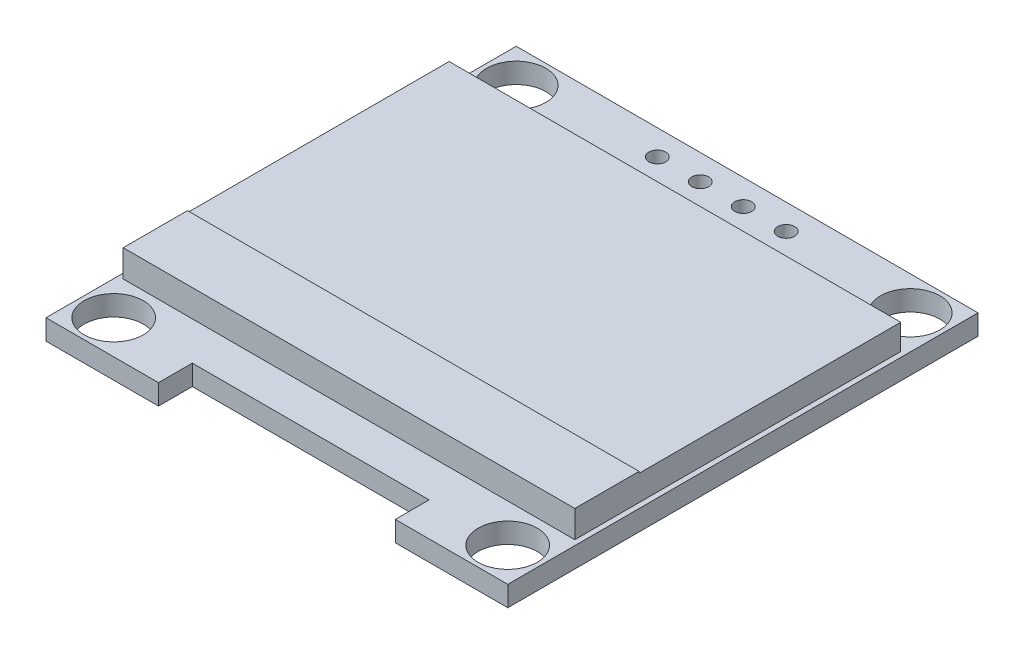
SolidWorks part; units mm, degrees
ref_plane "Plan de face" through (0, 0, 0) normal (0, 0, 1) x (1, 0, 0)
ref_plane "Plan de dessus" through (0, 0, 0) normal (0, 1, 0) x (1, 0, 0)
ref_plane "Plan de droite" through (0, 0, 0) normal (1, 0, 0) x (0, 0, -1)
sketch "Esquisse1" plane through (0, 0, 0) normal (0, 1, 0) x (1, 0, 0)
  line L0 (27.3, 0) -> (27.3, 2.0001) construction
  line L2 (0, 0) -> (0, 27.8)
  line L3 (0, 27.8) -> (27.3, 27.8)
  line L4 (27.3, 0) -> (27.3, 27.8)
  line L5 (0, 0) -> (0, 2.0001) construction
  line L6 (27.3, 2.0001) -> (0, 2.0001) construction
  line L7 (27.3, 2.0001) -> (25.2952, 2.0001) construction
  line L8 (0, 2.0001) -> (2.0027, 2.0001) construction
  line L9 (0, 27.8) -> (0, 25.8) construction
  line L10 (27.3, 27.8) -> (27.3, 25.8) construction
  line L11 (27.3, 25.8) -> (0, 25.8) construction
  line L12 (0, 25.8) -> (2, 25.8) construction
  line L13 (27.3, 25.8) -> (25.2952, 25.8) construction
  line L14 (27.3, 27.8) -> (27.3, 26.3) construction
  line L15 (0, 27.8) -> (0, 26.3) construction
  line L16 (0, 26.3) -> (27.3, 26.3) construction
  line L17 (0, 26.3) -> (9.84, 26.3) construction
  line L18 (27.3, 26.3) -> (17.46, 26.3) construction
  line L19 (9.84, 26.3) -> (12.38, 26.3) construction
  line L20 (12.38, 26.3) -> (14.92, 26.3) construction
  line L21 (0, 2.0001) -> (6.65, 2.0001) construction
  line L22 (27.3, 2.0001) -> (20.65, 2.0001) construction
  line L23 (6.65, 2.0001) -> (20.65, 2.0001)
  line L24 (6.65, 2.0001) -> (6.65, 0)
  line L25 (6.65, 0) -> (0, 0)
  line L26 (20.65, 2.0001) -> (20.65, 0)
  line L27 (20.65, 0) -> (27.3, 0)
  line L28 (2, 25.8) -> (25.2952, 2.0001) construction
  line L29 (25.2952, 25.8) -> (2.0027, 2.0001) construction
  circle A0 centre (25.2952, 2.0001) radius 1.75
  circle A1 centre (2.0027, 2.0001) radius 1.75
  circle A2 centre (25.2952, 25.8) radius 1.75
  circle A3 centre (2, 25.8) radius 1.75
  circle A4 centre (9.84, 26.3) radius 0.5
  circle A5 centre (17.46, 26.3) radius 0.5
  circle A6 centre (12.38, 26.3) radius 0.5
  circle A7 centre (14.92, 26.3) radius 0.5
extrude "Boss.-Extru.2" add sketch "Esquisse1" along normal blind 1.2
ref_plane "plan ecran" through (0, 1.2, 0) normal (0, 1, 0) x (1, 0, 0)
sketch "Esquisse9" plane through (0, 1.2, 0) normal (0, 1, 0) x (1, 0, 0)
  line L0 (2, 25.8) -> (25.2952, 2.0001) construction
  line L1 (25.2952, 25.8) -> (2.0027, 2.0001) construction
  line L3 (0.2976, 4.2661) -> (26.9976, 4.2661)
  line L4 (0.2976, 4.2661) -> (0.2976, 23.5341)
  line L5 (0.2976, 23.5341) -> (26.9976, 23.5341)
  line L6 (26.9976, 4.2661) -> (26.9976, 23.5341)
  line L7 (0.2976, 4.2661) -> (26.9976, 23.5341) construction
  line L8 (0.2976, 23.5341) -> (26.9976, 4.2661) construction
  point P8 (13.6476, 13.9001)
  dimension "D1" = 19.268
  dimension "D2" = 26.7
extrude "Boss.-Extru.3" add sketch "Esquisse9" along normal blind 1.5
sketch "Esquisse10" plane through (27.5069, 0, -25.3893) normal (0, -1, 0) x (-1, 0, 0)
  text T0 "OLED 0.96"
extrude "Enlèv. mat.-Extru.1" cut sketch "Esquisse10" against normal blind 0.5
sketch "Esquisse11" plane through (0, 2.7, 0) normal (0, 1, 0) x (1, 0, 0)
  line L1 (0.2976, 4.2661) -> (26.9976, 4.2661)
  line L2 (0.2976, 4.2661) -> (0.2976, 8.0659)
  line L3 (0.2976, 8.0659) -> (26.9976, 8.0659)
  line L4 (26.9976, 4.2661) -> (26.9976, 8.0659)
extrude "Boss.-Extru.4" add sketch "Esquisse11" along normal blind 0.1
